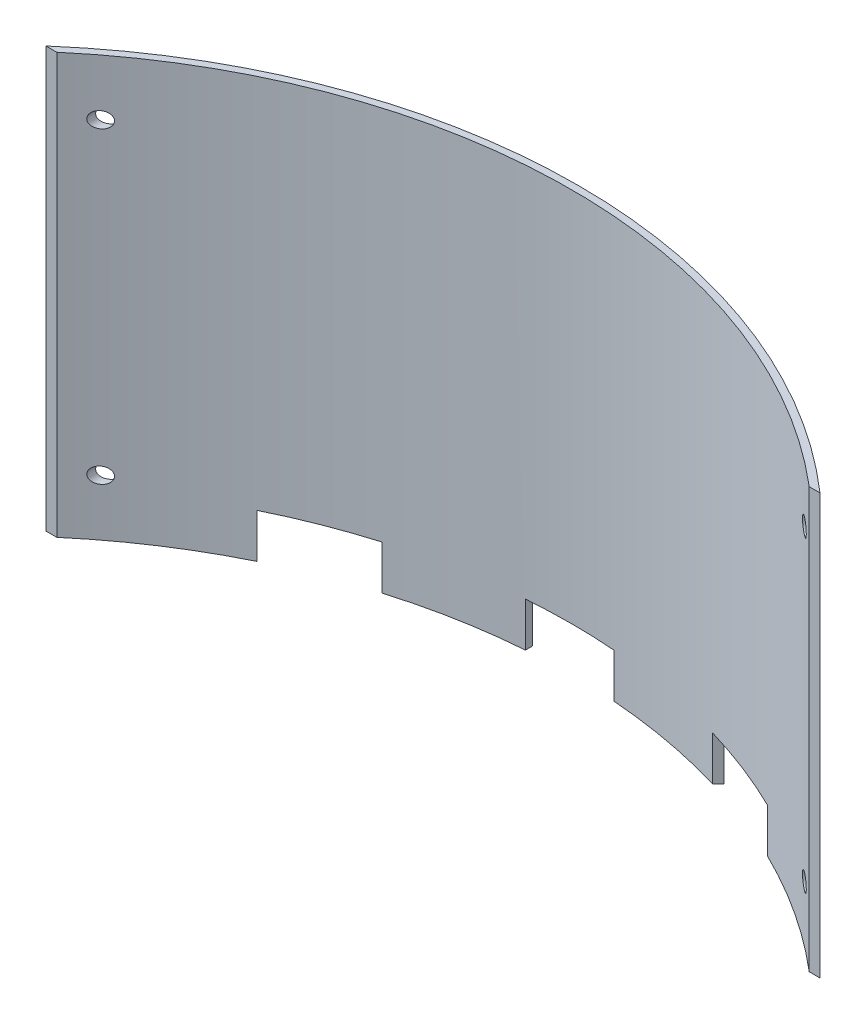
SolidWorks part; units mm, degrees
ref_plane "Front Plane" through (0, 0, 0) normal (0, 0, 1) x (1, 0, 0)
ref_plane "Top Plane" through (0, 0, 0) normal (0, 1, 0) x (1, 0, 0)
ref_plane "Right Plane" through (0, 0, 0) normal (1, 0, 0) x (0, 0, -1)
sketch "Sketch1" plane through (0, 0, 0) normal (0, 1, 0) x (1, 0, 0)
  line L0 (-170.1396, 0) -> (170.1396, 0) construction
  line L7 (170.1396, 0) -> (175, 0)
  line L17 (-175, 0) -> (-170.1396, 0)
  arc A2 (175, 0) -> (-175, 0) centre (0, -200.0147) ccw
  arc A3 (170.1396, 0) -> (-170.1396, 0) centre (0, -200.0147) ccw
  point P0 (0, 65.75)
  point P2 (0, 0)
  dimension "D2" = 3.175
  dimension "D3" = 65.75
  dimension "D1" = 350
extrude "Curved Plate" add sketch "Sketch1" along normal blind 190
sketch "Sketch2" plane through (0, 0, 0) normal (0, 1, 0) x (1, 0, 0)
  line L0 (0, 64.9964) -> (20, 64.9964) construction
  line L1 (-117.7623, 38.235) -> (-105.5219, 25.9946)
  line L2 (-105.5219, 25.9946) -> (-77.2377, 54.2789) construction
  line L3 (-175, 0) -> (-170.1396, 0) construction
  line L4 (-20, 64.9964) -> (-77.2377, 64.9964) construction
  line L5 (-77.2377, 64.9964) -> (-77.2377, 54.2789) construction
  line L6 (-117.7623, 38.235) -> (-175, 38.235) construction
  line L7 (-175, 38.235) -> (-175, 0) construction
  line L8 (0, 0) -> (0, 64.9964) construction
  line L11 (-77.2377, 54.2789) -> (-105.5219, 25.9946) construction
  line L12 (-77.2377, 54.2789) -> (-73.7021, 50.7433)
  line L13 (-105.5219, 25.9946) -> (-101.9864, 22.4591)
  line L14 (-73.7021, 50.7433) -> (-101.9864, 22.4591)
  line L19 (77.2377, 54.2789) -> (73.7021, 50.7433)
  line L20 (73.7021, 50.7433) -> (101.9864, 22.4591)
  line L21 (105.5219, 25.9946) -> (101.9864, 22.4591)
  line L22 (117.7623, 38.235) -> (105.5219, 25.9946)
  line L23 (-20, 64.9964) -> (0, 64.9964) construction
  line L24 (0, 64.9964) -> (20, 64.9964) construction
  line L25 (-20, 64.9964) -> (-20, 59.9964)
  line L26 (-20, 59.9964) -> (20, 59.9964)
  line L27 (20, 64.9964) -> (20, 59.9964)
  line L28 (-20, 64.9964) -> (0, 64.9964) construction
  line L29 (0, 64.9964) -> (0, 65.75) construction
  arc A0 (-117.7623, 38.235) -> (-77.2377, 54.2789) centre (0, -200.0147) cw
  arc A1 (175, 0) -> (-175, 0) centre (0, -200.0147) ccw construction
  arc A2 (117.7623, 38.235) -> (77.2377, 54.2789) centre (0, -200.0147) ccw
  arc A4 (-175, 0) -> (-117.7623, 38.235) centre (0, -200.0147) cw construction
  arc A5 (-77.2377, 54.2789) -> (-20, 64.9964) centre (0, -200.0147) cw construction
  arc A6 (-20, 64.9964) -> (20, 64.9964) centre (0, -200.0147) cw
  arc A7 (20, 64.9964) -> (77.2377, 54.2789) centre (0, -200.0147) cw construction
  arc A9 (117.7623, 38.235) -> (175, 0) centre (0, -200.0147) cw construction
  point P24 (0, 65.75)
  dimension "D1" = 40
  dimension "D2" = 135
  dimension "D3" = 40
  dimension "D4" = 5
  dimension "D5" = 5
extrude "IR Cutout" cut sketch "Sketch2" along normal blind 20
sketch "Sketch3" plane through (0, 0, 0) normal (0, 0, 1) x (1, 0, 0)
  line L0 (0, 190) -> (0, 0) construction
  line L1 (170.1396, 190) -> (-170.1396, 190) construction
  line L2 (-175, 190) -> (-175, 0) construction
  circle A0 centre (-159.125, 164.6) radius 3.5687
  circle A1 centre (-159.125, 25.4) radius 3.5687
  circle A2 centre (159.125, 25.4) radius 3.5687
  circle A3 centre (159.125, 164.6) radius 3.5687
  dimension "D1" = 7.1374
  dimension "D2" = 15.875
  dimension "D3" = 25.4
  dimension "D4" = 25.4
extrude "Mounting Holes" cut sketch "Sketch3" against normal through all
